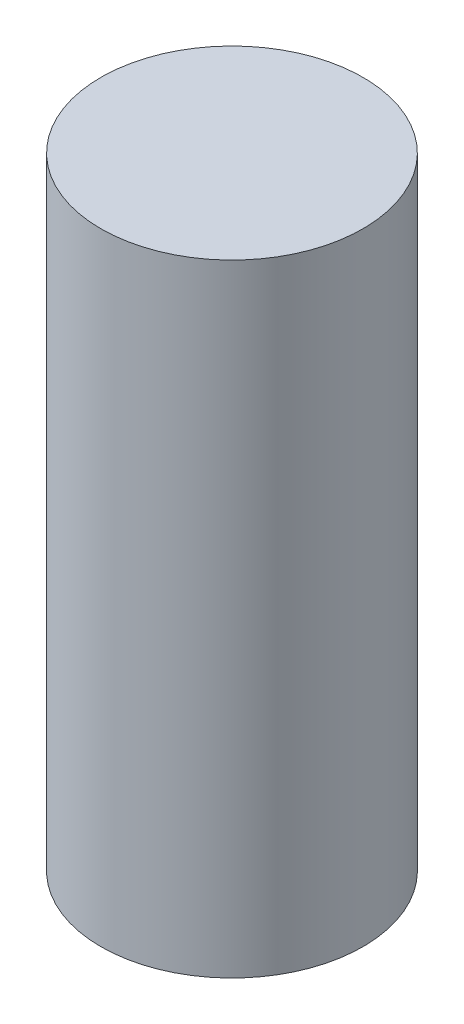
SolidWorks part; units mm, degrees
ref_plane "Front Plane" through (0, 0, 0) normal (0, 0, 1) x (1, 0, 0)
ref_plane "Top Plane" through (0, 0, 0) normal (0, 1, 0) x (1, 0, 0)
ref_plane "Right Plane" through (0, 0, 0) normal (1, 0, 0) x (0, 0, -1)
sketch "Sketch1" plane through (0, 0, 0) normal (0, 1, 0) x (1, 0, 0)
  circle A0 centre (0, 0) radius 6.1595
  dimension "D1" = 12.319
extrude "Boss-Extrude1" add sketch "Sketch1" along normal blind 29.21
